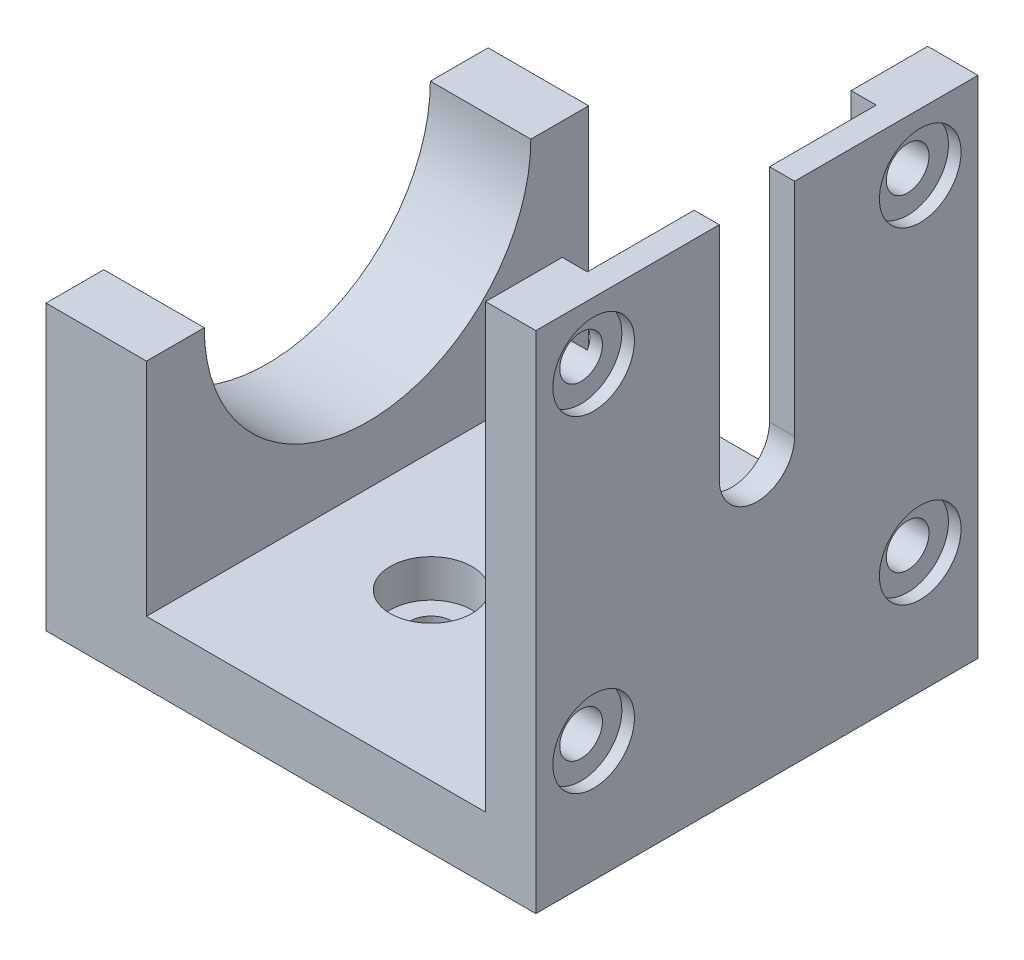
SolidWorks part; units mm, degrees
ref_plane "Front" through (0, 0, 0) normal (0, 0, 1) x (1, 0, 0)
ref_plane "Top" through (0, 0, 0) normal (0, 1, 0) x (1, 0, 0)
ref_plane "Right" through (0, 0, 0) normal (1, 0, 0) x (0, 0, -1)
sketch "Sketch1" plane through (0, 0, 0) normal (0, 1, 0) x (1, 0, 0)
  line L1 (0, 0) -> (39, 0)
  line L2 (0, 0) -> (0, 35.2)
  line L3 (0, 35.2) -> (39, 35.2)
  line L4 (39, 0) -> (39, 35.2)
  dimension "D1" = 35.2
  dimension "D2" = 39
extrude "Boss-Extrude1" add sketch "Sketch1" along normal blind 5
sketch "Sketch2" plane through (0, 5, 0) normal (0, 1, 0) x (1, 0, 0)
  line L0 (0, 0) -> (39, 0) construction
  line L1 (0, 35.2) -> (8, 35.2)
  line L2 (0, 35.2) -> (0, 0)
  line L3 (0, 0) -> (8, 0)
  line L4 (8, 35.2) -> (8, 0)
  dimension "D1" = 8
extrude "Boss-Extrude2" add sketch "Sketch2" along normal blind 35.2
sketch "Sketch3" plane through (0, 5, 0) normal (0, 1, 0) x (1, 0, 0)
  line L0 (39, 35.2) -> (8, 35.2) construction
  line L1 (39, 0) -> (35, 0)
  line L2 (39, 0) -> (39, 35.2)
  line L3 (39, 35.2) -> (35, 35.2)
  line L4 (35, 0) -> (35, 35.2)
  dimension "D1" = 4
extrude "Boss-Extrude3" add sketch "Sketch3" along normal blind 35.2
sketch "Sketch5" plane through (0, 0, 0) normal (-1, 0, 0) x (0, 0, 1)
  line L0 (-35.2, 40.2) -> (-35.2, 0) construction
  line L1 (-35.2, 40.2) -> (0, 40.2) construction
  circle A0 centre (-17.6, 22.6) radius 13
  dimension "D3" = 26
  dimension "D1" = 17.6
  dimension "D2" = 17.6
extrude "Cut-Extrude2" cut sketch "Sketch5" against normal up to next
hole_wizard "CBORE for M3 SHCS1" positions "Sketch8" profile "Sketch9" counterbore size "M3" standard "ANSI Metric" end condition up to next
sketch "Sketch8" plane through (0, 5, 0) normal (0, 1, 0) x (1, 0, 0)
  line L0 (35, 35.2) -> (35, 0) construction
  line L1 (35, 35.2) -> (8, 35.2) construction
  point P0 (17.507, 13.145)
  point P2 (17.5001, 22.145)
  point P4 (26.5, 22.1)
  point P6 (26.5, 13.145)
  dimension "D1" = 9
  dimension "D2" = 9
  dimension "D3" = 8.5
  dimension "D4" = 13.1
sketch "Sketch9" plane through (17.507, 5, -13.145) normal (1, 0, 0) x (0, 0, 1)
  line L0 (0, 0) -> (0, 5)
  line L1 (0, 5) -> (1.7, 5)
  line L3 (1.7, 5) -> (1.7, 3)
  line L4 (1.7, 3) -> (3.25, 3)
  line L5 (3.25, 3) -> (3.25, 0)
  line L7 (3.25, 0) -> (0, 0)
  line L11 (0, -6.35) -> (0, 107.95) construction
  dimension "Thru Hole Dia." = 3.4
  dimension "Thru Hole Depth" = 5
  dimension "C'Bore Dia." = 6.5
  dimension "C'Bore Depth" = 3
sketch "Sketch10" plane through (0, 40.2, 0) normal (0, 1, 0) x (1, 0, 0)
  line L0 (35, 35.2) -> (35, 0) construction
  line L5 (39, 0) -> (39, 35.2) construction
  line L6 (35, 0) -> (39, 0) construction
  line L7 (37, 20.6) -> (39, 20.6)
  line L8 (35, 29.1) -> (37, 29.1)
  line L9 (35, 29.1) -> (35, 6.1)
  line L10 (35, 6.1) -> (37, 6.1)
  line L13 (37, 14.6) -> (39, 14.6)
  line L14 (39, 20.6) -> (39, 14.6)
  line L15 (37, 29.1) -> (37, 20.6)
  line L16 (37, 14.6) -> (37, 6.1)
  dimension "D1" = 6
  dimension "D2" = 14.6
  dimension "D3" = 23
  dimension "D4" = 2
  dimension "D5" = 6.1
extrude "Cut-Extrude3" cut sketch "Sketch10" against normal blind 17.6
sketch "Sketch13" plane through (35, 0, 0) normal (-1, 0, 0) x (0, 0, 1)
  line L0 (-29.1, 22.6) -> (-6.1, 22.6) construction
  circle A0 centre (-17.6, 22.6) radius 3
  dimension "D1" = 6
extrude "Cut-Extrude5" cut sketch "Sketch13" against normal through all
sketch "Sketch14" plane through (35, 0, 0) normal (-1, 0, 0) x (0, 0, 1)
  circle A0 centre (-17.6, 22.6) radius 11.5
extrude "Cut-Extrude6" cut sketch "Sketch14" against normal blind 2
hole_wizard "CBORE for M3 SHCS2" positions "Sketch15" profile "Sketch16" counterbore size "M3" standard "ANSI Metric" end condition up to next
sketch "Sketch15" plane through (39, 0, 0) normal (1, 0, 0) x (0, 0, -1)
  arc A0 (14.6, 22.6) -> (20.6, 22.6) centre (17.6, 22.6) ccw construction
  point P0 (30.6, 35.6)
  point P2 (30.6, 9.6)
  point P4 (4.6, 9.6)
  point P6 (4.6, 35.6)
  dimension "D1" = 13
  dimension "D2" = 13
  dimension "D3" = 13
  dimension "D4" = 13
sketch "Sketch16" plane through (39, 35.6, -30.6) normal (0, 1, 0) x (0, 0, -1)
  line L0 (0, 0) -> (0, 4)
  line L1 (0, 4) -> (1.7, 4)
  line L3 (1.7, 4) -> (1.7, 1)
  line L4 (1.7, 1) -> (3.25, 1)
  line L5 (3.25, 1) -> (3.25, 0)
  line L7 (3.25, 0) -> (0, 0)
  line L11 (0, -6.35) -> (0, 107.95) construction
  dimension "Thru Hole Dia." = 3.4
  dimension "Thru Hole Depth" = 4
  dimension "C'Bore Dia." = 6.5
  dimension "C'Bore Depth" = 1
sketch "Sketch17" plane through (0, 40.2, 0) normal (0, 1, 0) x (1, 0, 0)
  line L1 (0, 35.2) -> (8, 35.2)
  line L2 (0, 35.2) -> (0, 0)
  line L3 (0, 0) -> (8, 0)
  line L4 (8, 35.2) -> (8, 0)
extrude "Cut-Extrude7" cut sketch "Sketch17" against normal blind 17.6
